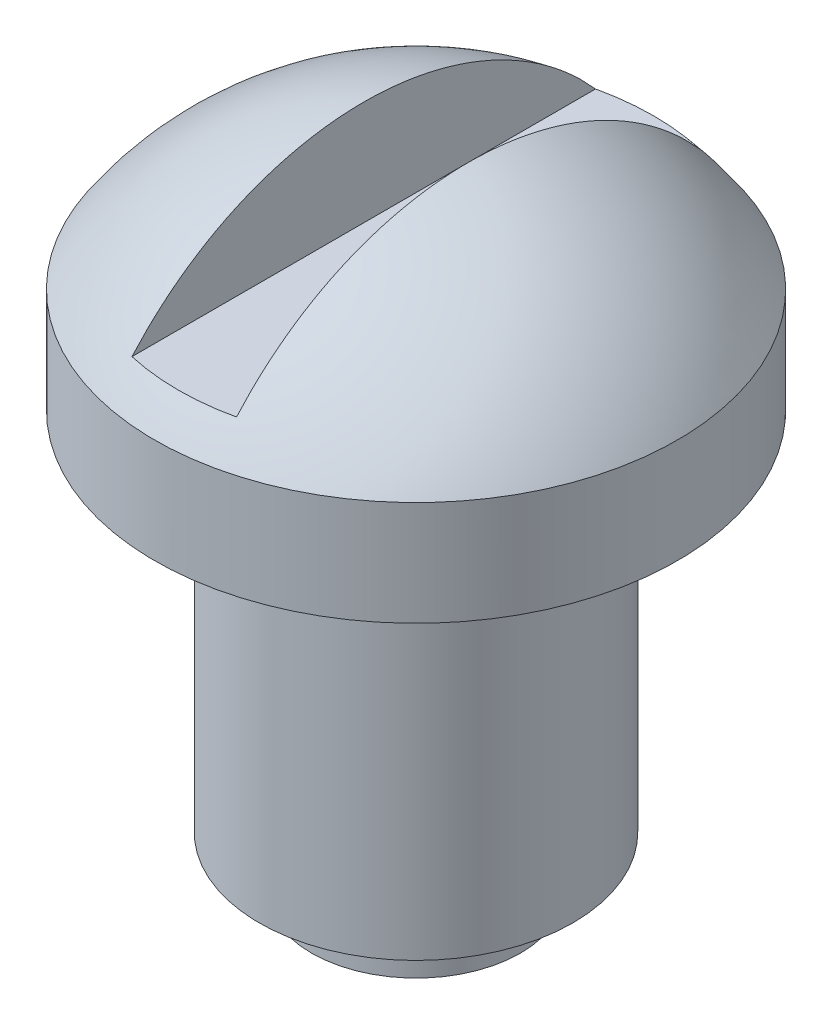
SolidWorks part; units mm, degrees
ref_plane "Front Plane" through (0, 0, 0) normal (0, 0, 1) x (1, 0, 0)
ref_plane "Top Plane" through (0, 0, 0) normal (0, 1, 0) x (1, 0, 0)
ref_plane "Right Plane" through (0, 0, 0) normal (1, 0, 0) x (0, 0, -1)
sketch "Sketch1" plane through (0, 0, 0) normal (0, 0, 1) x (1, 0, 0)
  line L0 (0, 3.6834) -> (0, -1) construction
  line L3 (0, -1) -> (5, -1)
  line L4 (5, 1) -> (5, -1)
  line L5 (0, 3.6834) -> (0, -1)
  arc A0 (5, 1) -> (0, 3.6834) centre (0, -2.3166) ccw
  point P0 (0, 0)
  dimension "D3" = 6
revolve "Revolve1" add sketch "Sketch1" angle 360 about L0
sketch "Sketch2" plane through (0, 0, 0) normal (0, 0, 1) x (1, 0, 0)
  line L0 (-1, 3.5995) -> (-1, 1.5995)
  line L1 (-1, 1.5995) -> (1, 1.5995)
  line L2 (0, 1.5995) -> (0, 3.6834) construction
  line L3 (1, 3.5995) -> (1, 1.5995)
  arc A0 (5, 1) -> (-5, 1) centre (0, -2.3166) ccw construction
  point P9 (0, 0)
  point P10 (0, 0)
  point P11 (0, 0)
  point P12 (0, 0)
  dimension "D1" = 1
  dimension "D2" = 2
extrude "Cut-Extrude5" cut sketch "Sketch2" against normal through all and the other way through all flip side to cut
sketch "Sketch3" plane through (0, -1, 0) normal (0, -1, 0) x (1, 0, 0)
  circle A0 centre (0, 0) radius 3
  dimension "D1" = 6
extrude "Boss-Extrude1" add sketch "Sketch3" along normal blind 7
sketch "Sketch4" plane through (0, -8, 0) normal (0, -1, 0) x (1, 0, 0)
  circle A0 centre (0, 0) radius 2
  dimension "D1" = 4
extrude "Boss-Extrude2" add sketch "Sketch4" along normal blind 1
